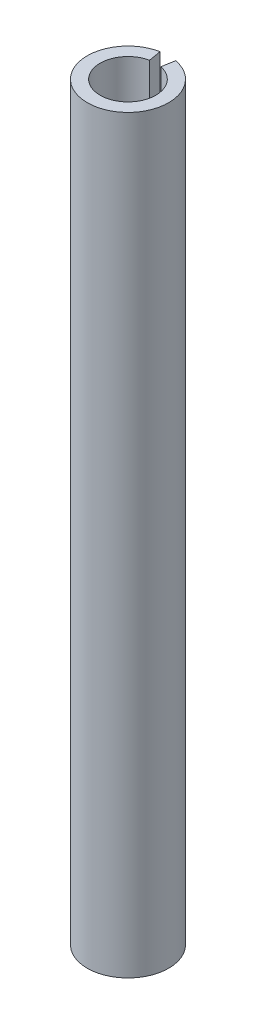
SolidWorks part; units mm, degrees
ref_plane "Front Plane" through (0, 0, 0) normal (0, 0, 1) x (1, 0, 0)
ref_plane "Top Plane" through (0, 0, 0) normal (0, 1, 0) x (1, 0, 0)
ref_plane "Right Plane" through (0, 0, 0) normal (1, 0, 0) x (0, 0, -1)
sketch "Sketch1" plane through (0, 0, 0) normal (0, 1, 0) x (1, 0, 0)
  circle A0 centre (0, 0) radius 6.5
  circle A1 centre (0, 0) radius 9.5
  dimension "D1" = 13
  dimension "D2" = 3
extrude "Boss-Extrude1" add sketch "Sketch1" along normal blind 175.02
sketch "Sketch2" plane through (0, 175.02, 0) normal (0, 1, 0) x (1, 0, 0)
  line L0 (0, 0) -> (0, 11.5) construction
  line L1 (0, 11.5) -> (-2.2, 11.5)
  line L2 (-2.2, 11.5) -> (-1.1, 5.0938)
  line L3 (-1.1, 5.0938) -> (1.1, 5.0938)
  line L4 (1.1, 5.0938) -> (2.2, 11.5)
  line L5 (2.2, 11.5) -> (0, 11.5)
  point P9 (0, 5.0938)
  dimension "D1" = 1.1
  dimension "D2" = 1.1
  dimension "D3" = 6.5
  dimension "D4" = 2.2
  dimension "D6" = 11.5
extrude "Cut-Extrude1" cut sketch "Sketch2" against normal through all both and the other way through all
